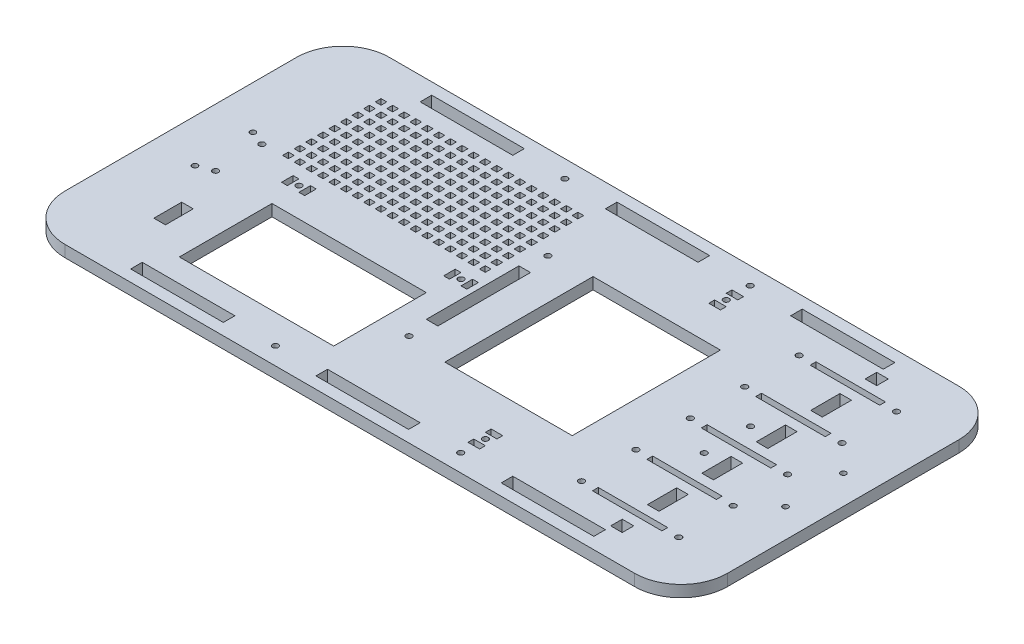
SolidWorks part; units mm, degrees
ref_plane "Front Plane" through (0, 0, 0) normal (0, 0, 1) x (1, 0, 0)
ref_plane "Top Plane" through (0, 0, 0) normal (0, 1, 0) x (1, 0, 0)
ref_plane "Right Plane" through (0, 0, 0) normal (1, 0, 0) x (0, 0, -1)
sketch "Sketch3" plane through (0, 0, 0) normal (0, 1, 0) x (1, 0, 0)
  line L1 (-156.21, -88.9) -> (156.21, -88.9)
  line L2 (-181.61, -63.5) -> (-181.61, 63.5)
  line L3 (-156.21, 88.9) -> (156.21, 88.9)
  line L4 (181.61, -63.5) -> (181.61, 63.5)
  line L5 (-181.61, -88.9) -> (181.61, 88.9) construction
  line L6 (-181.61, 88.9) -> (181.61, -88.9) construction
  arc A0 (156.21, -88.9) -> (181.61, -63.5) centre (156.21, -63.5) ccw
  arc A1 (156.21, 88.9) -> (181.61, 63.5) centre (156.21, 63.5) cw
  arc A2 (-156.21, -88.9) -> (-181.61, -63.5) centre (-156.21, -63.5) cw
  arc A3 (-181.61, 63.5) -> (-156.21, 88.9) centre (-156.21, 63.5) cw
  point P0 (0, 0)
  dimension "D3" = 25.4
  dimension "D1" = 177.8
  dimension "D2" = 363.22
extrude "BaseExtrude" add sketch "Sketch3" against normal blind 6.35
sketch "Sketch6" plane through (0, 0, 0) normal (0, 1, 0) x (1, 0, 0)
  line L0 (-181.61, 0) -> (181.61, 0) construction
  line L1 (-181.61, 63.5) -> (-181.61, -63.5) construction
  line L2 (181.61, -63.5) -> (181.61, 63.5) construction
  line L3 (0, -88.9) -> (0, 88.9) construction
  line L4 (-156.21, -88.9) -> (156.21, -88.9) construction
  line L5 (156.21, 88.9) -> (-156.21, 88.9) construction
  line L6 (3.937, 0) -> (3.937, 19.6413) construction
  circle A0 centre (-157.988, 15.875) radius 1.5
  circle A1 centre (-157.988, -15.875) radius 1.5
  circle A2 centre (165.862, -15.875) radius 1.5
  circle A3 centre (165.862, 15.875) radius 1.5
  dimension "D2" = 3
  dimension "D1" = 23.622
  dimension "D3" = 15.875
  dimension "D4" = 161.925
extrude "MainMountCut" cut sketch "Sketch6" against normal up to surface (6.35 mm away) up to face at (0, -6.35, 0)
sketch "Sketch7" plane through (0, 0, 0) normal (0, 1, 0) x (1, 0, 0)
  line L0 (76.6233, 79.375) -> (25.8233, 79.375) construction
  line L1 (127.4233, -82.55) -> (76.6233, -82.55)
  line L2 (127.4233, -82.55) -> (127.4233, -76.2)
  line L3 (127.4233, -76.2) -> (76.6233, -76.2)
  line L4 (76.6233, -82.55) -> (76.6233, -76.2)
  line L5 (25.8233, -82.55) -> (-24.9767, -82.55)
  line L6 (25.8233, -82.55) -> (25.8233, -76.2)
  line L7 (25.8233, -76.2) -> (-24.9767, -76.2)
  line L8 (-24.9767, -82.55) -> (-24.9767, -76.2)
  line L9 (-75.7767, -82.55) -> (-126.5767, -82.55)
  line L10 (-75.7767, -82.55) -> (-75.7767, -76.2)
  line L11 (-75.7767, -76.2) -> (-126.5767, -76.2)
  line L12 (-126.5767, -82.55) -> (-126.5767, -76.2)
  line L13 (127.4233, 76.2) -> (76.6233, 76.2)
  line L14 (127.4233, 76.2) -> (127.4233, 82.55)
  line L15 (127.4233, 82.55) -> (76.6233, 82.55)
  line L16 (76.6233, 76.2) -> (76.6233, 82.55)
  line L17 (25.8233, 76.2) -> (-24.9767, 76.2)
  line L18 (25.8233, 76.2) -> (25.8233, 82.55)
  line L19 (25.8233, 82.55) -> (-24.9767, 82.55)
  line L20 (-24.9767, 76.2) -> (-24.9767, 82.55)
  line L21 (-75.7767, 76.2) -> (-126.5767, 76.2)
  line L22 (-75.7767, 76.2) -> (-75.7767, 82.55)
  line L23 (-75.7767, 82.55) -> (-126.5767, 82.55)
  line L24 (-126.5767, 76.2) -> (-126.5767, 82.55)
  line L25 (-24.9767, 79.375) -> (-75.7767, 79.375) construction
  line L26 (-75.7767, -79.375) -> (-24.9767, -79.375) construction
  line L27 (76.6233, -79.375) -> (25.8233, -79.375) construction
  line L28 (181.61, -63.5) -> (181.61, 63.5) construction
  line L32 (-156.21, -88.9) -> (156.21, -88.9) construction
  line L35 (156.21, 88.9) -> (-156.21, 88.9) construction
  circle A0 centre (51.2233, 79.375) radius 1.6
  circle A1 centre (-50.3767, 79.375) radius 1.6
  circle A2 centre (-50.3767, -79.375) radius 1.6
  circle A3 centre (51.2233, -79.375) radius 1.6
  dimension "D5" = 3.2
  dimension "D1" = 50.8
  dimension "D2" = 6.35
  dimension "D3" = 6.35
  dimension "D4" = 6.35
  dimension "D6" = 54.1867
extrude "WallCut" cut sketch "Sketch7" against normal through all
sketch "Sketch8" plane through (0, 0, 0) normal (0, 1, 0) x (1, 0, 0)
  line L0 (124.46, -58.1025) -> (124.46, -31.4325) construction
  line L1 (143.51, -61.2775) -> (105.41, -61.2775)
  line L2 (143.51, -61.2775) -> (143.51, -58.1025)
  line L3 (143.51, -58.1025) -> (105.41, -58.1025)
  line L4 (105.41, -61.2775) -> (105.41, -58.1025)
  line L5 (143.51, -31.4325) -> (105.41, -31.4325)
  line L6 (143.51, -31.4325) -> (143.51, -28.2575)
  line L7 (143.51, -28.2575) -> (105.41, -28.2575)
  line L8 (105.41, -31.4325) -> (105.41, -28.2575)
  line L9 (143.51, -1.5875) -> (105.41, -1.5875)
  line L10 (143.51, -1.5875) -> (143.51, 1.5875)
  line L11 (143.51, 1.5875) -> (105.41, 1.5875)
  line L12 (105.41, -1.5875) -> (105.41, 1.5875)
  line L13 (143.51, 28.2575) -> (105.41, 28.2575)
  line L14 (143.51, 28.2575) -> (143.51, 31.4325)
  line L15 (143.51, 31.4325) -> (105.41, 31.4325)
  line L16 (105.41, 28.2575) -> (105.41, 31.4325)
  line L17 (143.51, 58.1025) -> (105.41, 58.1025)
  line L18 (143.51, 58.1025) -> (143.51, 61.2775)
  line L19 (143.51, 61.2775) -> (105.41, 61.2775)
  line L20 (105.41, 58.1025) -> (105.41, 61.2775)
  line L21 (124.46, -28.2575) -> (124.46, -1.5875) construction
  line L22 (124.46, -61.2775) -> (124.46, -76.2) construction
  line L23 (124.46, 1.5875) -> (124.46, 28.2575) construction
  line L24 (124.46, 31.4325) -> (124.46, 58.1025) construction
  line L25 (127.4233, -76.2) -> (76.6233, -76.2) construction
  line L26 (124.46, 61.2775) -> (124.46, 76.2) construction
  line L27 (76.6233, 76.2) -> (127.4233, 76.2) construction
  line L28 (181.61, -63.5) -> (181.61, 63.5) construction
  line L29 (143.51, -59.69) -> (151.13, -59.69) construction
  line L30 (151.13, -59.69) -> (151.13, 59.69) construction
  line L31 (151.13, 59.69) -> (143.51, 59.69) construction
  line L32 (143.51, 29.845) -> (151.13, 29.845) construction
  line L33 (143.51, 0) -> (151.13, 0) construction
  line L34 (143.51, -29.845) -> (151.13, -29.845) construction
  line L35 (105.41, -59.69) -> (97.79, -59.69) construction
  line L36 (97.79, -59.69) -> (97.79, 59.69) construction
  line L37 (97.79, 59.69) -> (105.41, 59.69) construction
  line L38 (105.41, 29.845) -> (97.79, 29.845) construction
  line L39 (105.41, 0) -> (97.79, 0) construction
  line L40 (105.41, -29.845) -> (97.79, -29.845) construction
  circle A0 centre (151.13, -59.69) radius 1.6
  circle A1 centre (151.13, -29.845) radius 1.6
  circle A2 centre (151.13, 0) radius 1.6
  circle A3 centre (151.13, 29.845) radius 1.6
  circle A4 centre (151.13, 59.69) radius 1.6
  circle A5 centre (97.79, 59.69) radius 1.6
  circle A6 centre (97.79, 29.845) radius 1.6
  circle A7 centre (97.79, 0) radius 1.6
  circle A8 centre (97.79, -29.845) radius 1.6
  circle A9 centre (97.79, -59.69) radius 1.6
  dimension "D6" = 3.2
  dimension "D1" = 3.175
  dimension "D2" = 26.67
  dimension "D3" = 38.1
  dimension "D4" = 57.15
  dimension "D5" = 7.62
extrude "WireMountCut" cut sketch "Sketch8" against normal through all
sketch "Sketch9" plane through (0, 0, 0) normal (0, 1, 0) x (1, 0, 0)
  line L0 (118.11, -12.7) -> (118.11, 12.7) construction
  line L1 (-149.86, -12.7) -> (-149.86, 12.7) construction
  line L2 (-149.86, 12.7) -> (118.11, 12.7) construction
  line L3 (118.11, -12.7) -> (-149.86, -12.7) construction
  line L4 (118.11, -12.7) -> (118.11, -88.9) construction
  line L5 (-156.21, -88.9) -> (156.21, -88.9) construction
  line L6 (118.11, 12.7) -> (118.11, 88.9) construction
  line L7 (156.21, 88.9) -> (-156.21, 88.9) construction
  line L8 (-181.61, 63.5) -> (-181.61, -63.5) construction
  line L9 (181.61, -63.5) -> (181.61, 63.5) construction
  circle A0 centre (118.11, 12.7) radius 1.6
  circle A1 centre (118.11, -12.7) radius 1.6
  circle A2 centre (-149.86, -12.7) radius 1.6
  circle A3 centre (-149.86, 12.7) radius 1.6
  dimension "D1" = 3.2
  dimension "D2" = 76.2
  dimension "D3" = 31.75
  dimension "D4" = 63.5
extrude "Cut-Extrude3" cut sketch "Sketch9" against normal through all
sketch "Sketch11" plane through (0, 0, 0) normal (0, 1, 0) x (1, 0, 0)
  line L0 (54.61, 72.39) -> (48.26, 72.39)
  line L1 (54.61, -69.215) -> (54.61, -62.865) construction
  line L2 (54.61, 59.69) -> (48.26, 59.69)
  line L3 (54.61, -72.39) -> (54.61, -69.215)
  line L4 (54.61, -69.215) -> (48.26, -69.215)
  line L5 (181.61, 0) -> (-181.61, 0) construction
  line L6 (181.61, -63.5) -> (181.61, 63.5) construction
  line L7 (-181.61, 63.5) -> (-181.61, -63.5) construction
  line L8 (51.435, 66.04) -> (51.435, 62.865) construction
  line L9 (-15.24, -25.4) -> (-21.59, -25.4)
  line L10 (-15.24, -25.4) -> (-15.24, 25.4)
  line L11 (-15.24, 25.4) -> (-21.59, 25.4)
  line L12 (-21.59, -25.4) -> (-21.59, 25.4)
  line L13 (48.26, -72.39) -> (48.26, -69.215)
  line L14 (54.61, -62.865) -> (48.26, -62.865)
  line L15 (54.61, -62.865) -> (54.61, -59.69)
  line L17 (48.26, -62.865) -> (48.26, -59.69)
  line L18 (51.435, -69.215) -> (51.435, -66.04) construction
  line L19 (48.26, -69.215) -> (48.26, -62.865) construction
  line L20 (51.435, -66.04) -> (51.435, -62.865) construction
  line L22 (48.26, 69.215) -> (48.26, 62.865) construction
  line L23 (51.435, 69.215) -> (51.435, 66.04) construction
  line L24 (54.61, 69.215) -> (54.61, 62.865) construction
  line L25 (48.26, 62.865) -> (48.26, 59.69)
  line L27 (54.61, 62.865) -> (54.61, 59.69)
  line L28 (54.61, 62.865) -> (48.26, 62.865)
  line L29 (48.26, 72.39) -> (48.26, 69.215)
  line L30 (54.61, 69.215) -> (48.26, 69.215)
  line L31 (54.61, 72.39) -> (54.61, 69.215)
  line L33 (51.435, -66.04) -> (51.435, -62.865) construction
  line L34 (-18.415, -25.4) -> (-18.415, -38.1) construction
  line L35 (-18.415, 25.4) -> (-18.415, 38.1) construction
  line L36 (54.61, -72.39) -> (48.26, -72.39)
  line L37 (54.61, -59.69) -> (48.26, -59.69)
  circle A0 centre (51.435, -66.04) radius 1.6
  circle A1 centre (51.435, 66.04) radius 1.6
  circle A2 centre (-18.415, -38.1) radius 1.6
  circle A3 centre (-18.415, 38.1) radius 1.6
  point P45 (-15.24, 0)
  dimension "D4" = 50.8
  dimension "D2" = 3.2
  dimension "D9" = 3.2
  dimension "D1" = 12.7
  dimension "D6" = 63.5
  dimension "D7" = 50.8
  dimension "D8" = 12.7
extrude "Cut-Extrude4" cut sketch "Sketch11" against normal through all
sketch "Sketch13" plane through (0, 0, 0) normal (0, 1, 0) x (1, 0, 0)
  line L0 (-123.2154, 6.35) -> (-116.8654, 6.35) construction
  line L1 (-24.7904, 6.35) -> (-27.9654, 6.35)
  line L2 (-24.7904, 6.35) -> (-24.7904, 0)
  line L3 (-24.7904, 0) -> (-27.9654, 0)
  line L4 (-27.9654, 6.35) -> (-27.9654, 0)
  line L5 (-34.3154, 6.35) -> (-37.4904, 6.35)
  line L6 (-34.3154, 6.35) -> (-34.3154, 0)
  line L7 (-34.3154, 0) -> (-37.4904, 0)
  line L8 (-37.4904, 6.35) -> (-37.4904, 0)
  line L9 (-113.6904, 0) -> (-116.8654, 0)
  line L10 (-113.6904, 0) -> (-113.6904, 6.35)
  line L11 (-113.6904, 6.35) -> (-116.8654, 6.35)
  line L12 (-116.8654, 0) -> (-116.8654, 6.35)
  line L13 (-123.2154, 0) -> (-126.3904, 0)
  line L14 (-123.2154, 0) -> (-123.2154, 6.35)
  line L15 (-123.2154, 6.35) -> (-126.3904, 6.35)
  line L16 (-126.3904, 0) -> (-126.3904, 6.35)
  line L17 (-123.2154, 0) -> (-116.8654, 0) construction
  line L18 (-34.3154, 0) -> (-27.9654, 0) construction
  line L19 (-34.3154, 6.35) -> (-27.9654, 6.35) construction
  line L20 (-34.3154, 3.175) -> (-31.1404, 3.175) construction
  line L21 (-31.1404, 3.175) -> (-27.9654, 3.175) construction
  line L22 (-123.2154, 3.175) -> (-120.0404, 3.175) construction
  line L23 (-120.0404, 3.175) -> (-116.8654, 3.175) construction
  line L25 (-75.7767, -76.2) -> (-126.5767, -76.2) construction
  line L26 (-21.59, 25.4) -> (-21.59, -25.4) construction
  circle A0 centre (-120.0404, 3.175) radius 1.6
  circle A1 centre (-31.1404, 3.175) radius 1.6
  dimension "D3" = 3.2
  dimension "D1" = 3.175
  dimension "D2" = 6.35
  dimension "D4" = 76.2
  dimension "D5" = 6.35
  dimension "D6" = 3.2004
  dimension "D7" = 88.9
extrude "Cut-Extrude5" cut sketch "Sketch13" against normal through all
sketch "Sketch14" plane through (0, 0, 0) normal (0, 1, 0) x (1, 0, 0)
  line L0 (-137.9819, -44.45) -> (-144.3319, -44.45) construction
  line L1 (-137.9819, -52.07) -> (-144.3319, -52.07)
  line L2 (-137.9819, -52.07) -> (-137.9819, -36.83)
  line L3 (-137.9819, -36.83) -> (-144.3319, -36.83)
  line L4 (-144.3319, -52.07) -> (-144.3319, -36.83)
  line L5 (-75.7767, -76.2) -> (-126.5767, -76.2) construction
  line L6 (-181.61, 63.5) -> (-181.61, -63.5) construction
  dimension "D1" = 15.24
  dimension "D2" = 6.35
  dimension "D3" = 31.75
  dimension "D4" = 37.2781
extrude "Cut-Extrude6" cut sketch "Sketch14" against normal through all
ref_plane "Plane1" through (0, 0, 44.45) normal (0, 0, -1) x (-1, 0, 0)
sketch "Sketch15" plane through (0, 0, 0) normal (0, 1, 0) x (1, 0, 0)
  line L0 (181.61, 0) -> (73.66, 0) construction
  line L1 (73.66, 40.64) -> (3.81, 40.64)
  line L2 (73.66, 40.64) -> (73.66, -40.64)
  line L3 (73.66, -40.64) -> (3.81, -40.64)
  line L4 (3.81, 40.64) -> (3.81, -40.64)
  line L5 (181.61, -63.5) -> (181.61, 63.5) construction
  line L6 (48.26, 59.69) -> (54.61, 59.69) construction
  line L7 (-15.24, -25.4) -> (-15.24, 25.4) construction
  line L8 (-37.4904, 0) -> (-34.3154, 0) construction
  line L9 (-34.29, -12.7) -> (-118.9319, -12.7)
  line L10 (-34.29, -12.7) -> (-34.29, -63.5)
  line L11 (-34.29, -63.5) -> (-118.9319, -63.5)
  line L12 (-118.9319, -12.7) -> (-118.9319, -63.5)
  line L13 (-75.7767, -76.2) -> (-126.5767, -76.2) construction
  line L14 (-137.9819, -52.07) -> (-137.9819, -36.83) construction
  line L15 (-21.59, 25.4) -> (-21.59, -25.4) construction
  line L16 (-34.0808, 67.0276) -> (-34.0808, 63.8526)
  line L17 (-27.7308, 67.0276) -> (-30.9058, 67.0276)
  line L18 (-27.7308, 67.0276) -> (-27.7308, 63.8526)
  line L19 (-27.7308, 63.8526) -> (-30.9058, 63.8526)
  line L20 (-30.9058, 67.0276) -> (-30.9058, 63.8526)
  line L21 (-34.0808, 67.0276) -> (-37.2558, 67.0276)
  line L22 (-37.2558, 67.0276) -> (-37.2558, 63.8526)
  line L23 (-34.0808, 63.8526) -> (-37.2558, 63.8526)
  line L24 (-40.4308, 67.0276) -> (-40.4308, 63.8526)
  line L25 (-40.4308, 67.0276) -> (-43.6058, 67.0276)
  line L26 (-43.6058, 67.0276) -> (-43.6058, 63.8526)
  line L27 (-40.4308, 63.8526) -> (-43.6058, 63.8526)
  line L28 (-46.7808, 67.0276) -> (-46.7808, 63.8526)
  line L29 (-46.7808, 67.0276) -> (-49.9558, 67.0276)
  line L30 (-49.9558, 67.0276) -> (-49.9558, 63.8526)
  line L31 (-46.7808, 63.8526) -> (-49.9558, 63.8526)
  line L32 (-53.1308, 67.0276) -> (-53.1308, 63.8526)
  line L33 (-53.1308, 67.0276) -> (-56.3058, 67.0276)
  line L34 (-56.3058, 67.0276) -> (-56.3058, 63.8526)
  line L35 (-53.1308, 63.8526) -> (-56.3058, 63.8526)
  line L36 (-59.4808, 67.0276) -> (-59.4808, 63.8526)
  line L37 (-59.4808, 67.0276) -> (-62.6558, 67.0276)
  line L38 (-62.6558, 67.0276) -> (-62.6558, 63.8526)
  line L39 (-59.4808, 63.8526) -> (-62.6558, 63.8526)
  line L40 (-65.8308, 67.0276) -> (-65.8308, 63.8526)
  line L41 (-65.8308, 67.0276) -> (-69.0058, 67.0276)
  line L42 (-69.0058, 67.0276) -> (-69.0058, 63.8526)
  line L43 (-65.8308, 63.8526) -> (-69.0058, 63.8526)
  line L44 (-72.1808, 67.0276) -> (-72.1808, 63.8526)
  line L45 (-72.1808, 67.0276) -> (-75.3558, 67.0276)
  line L46 (-75.3558, 67.0276) -> (-75.3558, 63.8526)
  line L47 (-72.1808, 63.8526) -> (-75.3558, 63.8526)
  line L48 (-78.5308, 67.0276) -> (-78.5308, 63.8526)
  line L49 (-78.5308, 67.0276) -> (-81.7058, 67.0276)
  line L50 (-81.7058, 67.0276) -> (-81.7058, 63.8526)
  line L51 (-78.5308, 63.8526) -> (-81.7058, 63.8526)
  line L52 (-84.8808, 67.0276) -> (-84.8808, 63.8526)
  line L53 (-84.8808, 67.0276) -> (-88.0558, 67.0276)
  line L54 (-88.0558, 67.0276) -> (-88.0558, 63.8526)
  line L55 (-84.8808, 63.8526) -> (-88.0558, 63.8526)
  line L56 (-91.2308, 67.0276) -> (-91.2308, 63.8526)
  line L57 (-91.2308, 67.0276) -> (-94.4058, 67.0276)
  line L58 (-94.4058, 67.0276) -> (-94.4058, 63.8526)
  line L59 (-91.2308, 63.8526) -> (-94.4058, 63.8526)
  line L60 (-97.5808, 67.0276) -> (-97.5808, 63.8526)
  line L61 (-97.5808, 67.0276) -> (-100.7558, 67.0276)
  line L62 (-100.7558, 67.0276) -> (-100.7558, 63.8526)
  line L63 (-97.5808, 63.8526) -> (-100.7558, 63.8526)
  line L64 (-103.9308, 67.0276) -> (-103.9308, 63.8526)
  line L65 (-103.9308, 67.0276) -> (-107.1058, 67.0276)
  line L66 (-107.1058, 67.0276) -> (-107.1058, 63.8526)
  line L67 (-103.9308, 63.8526) -> (-107.1058, 63.8526)
  line L68 (-110.2808, 67.0276) -> (-110.2808, 63.8526)
  line L69 (-110.2808, 67.0276) -> (-113.4558, 67.0276)
  line L70 (-113.4558, 67.0276) -> (-113.4558, 63.8526)
  line L71 (-110.2808, 63.8526) -> (-113.4558, 63.8526)
  line L72 (-116.6308, 67.0276) -> (-116.6308, 63.8526)
  line L73 (-116.6308, 67.0276) -> (-119.8058, 67.0276)
  line L74 (-119.8058, 67.0276) -> (-119.8058, 63.8526)
  line L75 (-116.6308, 63.8526) -> (-119.8058, 63.8526)
  line L76 (-122.9808, 67.0276) -> (-122.9808, 63.8526)
  line L77 (-122.9808, 67.0276) -> (-126.1558, 67.0276)
  line L78 (-126.1558, 67.0276) -> (-126.1558, 63.8526)
  line L79 (-122.9808, 63.8526) -> (-126.1558, 63.8526)
  line L80 (-129.3308, 67.0276) -> (-129.3308, 63.8526)
  line L81 (-129.3308, 67.0276) -> (-132.5058, 67.0276)
  line L82 (-132.5058, 67.0276) -> (-132.5058, 63.8526)
  line L83 (-129.3308, 63.8526) -> (-132.5058, 63.8526)
  line L84 (-135.6808, 67.0276) -> (-135.6808, 63.8526)
  line L85 (-135.6808, 67.0276) -> (-138.8558, 67.0276)
  line L86 (-138.8558, 67.0276) -> (-138.8558, 63.8526)
  line L87 (-135.6808, 63.8526) -> (-138.8558, 63.8526)
  line L88 (-34.0808, 60.6776) -> (-34.0808, 57.5026)
  line L89 (-34.0808, 60.6776) -> (-37.2558, 60.6776)
  line L90 (-37.2558, 60.6776) -> (-37.2558, 57.5026)
  line L91 (-34.0808, 57.5026) -> (-37.2558, 57.5026)
  line L92 (-40.4308, 60.6776) -> (-40.4308, 57.5026)
  line L93 (-40.4308, 60.6776) -> (-43.6058, 60.6776)
  line L94 (-43.6058, 60.6776) -> (-43.6058, 57.5026)
  line L95 (-40.4308, 57.5026) -> (-43.6058, 57.5026)
  line L96 (-46.7808, 60.6776) -> (-46.7808, 57.5026)
  line L97 (-46.7808, 60.6776) -> (-49.9558, 60.6776)
  line L98 (-49.9558, 60.6776) -> (-49.9558, 57.5026)
  line L99 (-46.7808, 57.5026) -> (-49.9558, 57.5026)
  line L100 (-53.1308, 60.6776) -> (-53.1308, 57.5026)
  line L101 (-53.1308, 60.6776) -> (-56.3058, 60.6776)
  line L102 (-56.3058, 60.6776) -> (-56.3058, 57.5026)
  line L103 (-53.1308, 57.5026) -> (-56.3058, 57.5026)
  line L104 (-59.4808, 60.6776) -> (-59.4808, 57.5026)
  line L105 (-59.4808, 60.6776) -> (-62.6558, 60.6776)
  line L106 (-62.6558, 60.6776) -> (-62.6558, 57.5026)
  line L107 (-59.4808, 57.5026) -> (-62.6558, 57.5026)
  line L108 (-65.8308, 60.6776) -> (-65.8308, 57.5026)
  line L109 (-65.8308, 60.6776) -> (-69.0058, 60.6776)
  line L110 (-69.0058, 60.6776) -> (-69.0058, 57.5026)
  line L111 (-65.8308, 57.5026) -> (-69.0058, 57.5026)
  line L112 (-72.1808, 60.6776) -> (-72.1808, 57.5026)
  line L113 (-72.1808, 60.6776) -> (-75.3558, 60.6776)
  line L114 (-75.3558, 60.6776) -> (-75.3558, 57.5026)
  line L115 (-72.1808, 57.5026) -> (-75.3558, 57.5026)
  line L116 (-78.5308, 60.6776) -> (-78.5308, 57.5026)
  line L117 (-78.5308, 60.6776) -> (-81.7058, 60.6776)
  line L118 (-81.7058, 60.6776) -> (-81.7058, 57.5026)
  line L119 (-78.5308, 57.5026) -> (-81.7058, 57.5026)
  line L120 (-84.8808, 60.6776) -> (-84.8808, 57.5026)
  line L121 (-84.8808, 60.6776) -> (-88.0558, 60.6776)
  line L122 (-88.0558, 60.6776) -> (-88.0558, 57.5026)
  line L123 (-84.8808, 57.5026) -> (-88.0558, 57.5026)
  line L124 (-91.2308, 60.6776) -> (-91.2308, 57.5026)
  line L125 (-91.2308, 60.6776) -> (-94.4058, 60.6776)
  line L126 (-94.4058, 60.6776) -> (-94.4058, 57.5026)
  line L127 (-91.2308, 57.5026) -> (-94.4058, 57.5026)
  line L128 (-97.5808, 60.6776) -> (-97.5808, 57.5026)
  line L129 (-97.5808, 60.6776) -> (-100.7558, 60.6776)
  line L130 (-100.7558, 60.6776) -> (-100.7558, 57.5026)
  line L131 (-97.5808, 57.5026) -> (-100.7558, 57.5026)
  line L132 (-103.9308, 60.6776) -> (-103.9308, 57.5026)
  line L133 (-103.9308, 60.6776) -> (-107.1058, 60.6776)
  line L134 (-107.1058, 60.6776) -> (-107.1058, 57.5026)
  line L135 (-103.9308, 57.5026) -> (-107.1058, 57.5026)
  line L136 (-110.2808, 60.6776) -> (-110.2808, 57.5026)
  line L137 (-110.2808, 60.6776) -> (-113.4558, 60.6776)
  line L138 (-113.4558, 60.6776) -> (-113.4558, 57.5026)
  line L139 (-110.2808, 57.5026) -> (-113.4558, 57.5026)
  line L140 (-116.6308, 60.6776) -> (-116.6308, 57.5026)
  line L141 (-116.6308, 60.6776) -> (-119.8058, 60.6776)
  line L142 (-119.8058, 60.6776) -> (-119.8058, 57.5026)
  line L143 (-116.6308, 57.5026) -> (-119.8058, 57.5026)
  line L144 (-122.9808, 60.6776) -> (-122.9808, 57.5026)
  line L145 (-122.9808, 60.6776) -> (-126.1558, 60.6776)
  line L146 (-126.1558, 60.6776) -> (-126.1558, 57.5026)
  line L147 (-122.9808, 57.5026) -> (-126.1558, 57.5026)
  line L148 (-129.3308, 60.6776) -> (-129.3308, 57.5026)
  line L149 (-129.3308, 60.6776) -> (-132.5058, 60.6776)
  line L150 (-132.5058, 60.6776) -> (-132.5058, 57.5026)
  line L151 (-129.3308, 57.5026) -> (-132.5058, 57.5026)
  line L152 (-135.6808, 60.6776) -> (-135.6808, 57.5026)
  line L153 (-135.6808, 60.6776) -> (-138.8558, 60.6776)
  line L154 (-138.8558, 60.6776) -> (-138.8558, 57.5026)
  line L155 (-135.6808, 57.5026) -> (-138.8558, 57.5026)
  line L156 (-34.0808, 54.3276) -> (-34.0808, 51.1526)
  line L157 (-34.0808, 54.3276) -> (-37.2558, 54.3276)
  line L158 (-37.2558, 54.3276) -> (-37.2558, 51.1526)
  line L159 (-34.0808, 51.1526) -> (-37.2558, 51.1526)
  line L160 (-40.4308, 54.3276) -> (-40.4308, 51.1526)
  line L161 (-40.4308, 54.3276) -> (-43.6058, 54.3276)
  line L162 (-43.6058, 54.3276) -> (-43.6058, 51.1526)
  line L163 (-40.4308, 51.1526) -> (-43.6058, 51.1526)
  line L164 (-46.7808, 54.3276) -> (-46.7808, 51.1526)
  line L165 (-46.7808, 54.3276) -> (-49.9558, 54.3276)
  line L166 (-49.9558, 54.3276) -> (-49.9558, 51.1526)
  line L167 (-46.7808, 51.1526) -> (-49.9558, 51.1526)
  line L168 (-53.1308, 54.3276) -> (-53.1308, 51.1526)
  line L169 (-53.1308, 54.3276) -> (-56.3058, 54.3276)
  line L170 (-56.3058, 54.3276) -> (-56.3058, 51.1526)
  line L171 (-53.1308, 51.1526) -> (-56.3058, 51.1526)
  line L172 (-59.4808, 54.3276) -> (-59.4808, 51.1526)
  line L173 (-59.4808, 54.3276) -> (-62.6558, 54.3276)
  line L174 (-62.6558, 54.3276) -> (-62.6558, 51.1526)
  line L175 (-59.4808, 51.1526) -> (-62.6558, 51.1526)
  line L176 (-65.8308, 54.3276) -> (-65.8308, 51.1526)
  line L177 (-65.8308, 54.3276) -> (-69.0058, 54.3276)
  line L178 (-69.0058, 54.3276) -> (-69.0058, 51.1526)
  line L179 (-65.8308, 51.1526) -> (-69.0058, 51.1526)
  line L180 (-72.1808, 54.3276) -> (-72.1808, 51.1526)
  line L181 (-72.1808, 54.3276) -> (-75.3558, 54.3276)
  line L182 (-75.3558, 54.3276) -> (-75.3558, 51.1526)
  line L183 (-72.1808, 51.1526) -> (-75.3558, 51.1526)
  line L184 (-78.5308, 54.3276) -> (-78.5308, 51.1526)
  line L185 (-78.5308, 54.3276) -> (-81.7058, 54.3276)
  line L186 (-81.7058, 54.3276) -> (-81.7058, 51.1526)
  line L187 (-78.5308, 51.1526) -> (-81.7058, 51.1526)
  line L188 (-84.8808, 54.3276) -> (-84.8808, 51.1526)
  line L189 (-84.8808, 54.3276) -> (-88.0558, 54.3276)
  line L190 (-88.0558, 54.3276) -> (-88.0558, 51.1526)
  line L191 (-84.8808, 51.1526) -> (-88.0558, 51.1526)
  line L192 (-91.2308, 54.3276) -> (-91.2308, 51.1526)
  line L193 (-91.2308, 54.3276) -> (-94.4058, 54.3276)
  line L194 (-94.4058, 54.3276) -> (-94.4058, 51.1526)
  line L195 (-91.2308, 51.1526) -> (-94.4058, 51.1526)
  line L196 (-97.5808, 54.3276) -> (-97.5808, 51.1526)
  line L197 (-97.5808, 54.3276) -> (-100.7558, 54.3276)
  line L198 (-100.7558, 54.3276) -> (-100.7558, 51.1526)
  line L199 (-97.5808, 51.1526) -> (-100.7558, 51.1526)
  line L200 (-103.9308, 54.3276) -> (-103.9308, 51.1526)
  line L201 (-103.9308, 54.3276) -> (-107.1058, 54.3276)
  line L202 (-107.1058, 54.3276) -> (-107.1058, 51.1526)
  line L203 (-103.9308, 51.1526) -> (-107.1058, 51.1526)
  line L204 (-110.2808, 54.3276) -> (-110.2808, 51.1526)
  line L205 (-110.2808, 54.3276) -> (-113.4558, 54.3276)
  line L206 (-113.4558, 54.3276) -> (-113.4558, 51.1526)
  line L207 (-110.2808, 51.1526) -> (-113.4558, 51.1526)
  line L208 (-116.6308, 54.3276) -> (-116.6308, 51.1526)
  line L209 (-116.6308, 54.3276) -> (-119.8058, 54.3276)
  line L210 (-119.8058, 54.3276) -> (-119.8058, 51.1526)
  line L211 (-116.6308, 51.1526) -> (-119.8058, 51.1526)
  line L212 (-122.9808, 54.3276) -> (-122.9808, 51.1526)
  line L213 (-122.9808, 54.3276) -> (-126.1558, 54.3276)
  line L214 (-126.1558, 54.3276) -> (-126.1558, 51.1526)
  line L215 (-122.9808, 51.1526) -> (-126.1558, 51.1526)
  line L216 (-129.3308, 54.3276) -> (-129.3308, 51.1526)
  line L217 (-129.3308, 54.3276) -> (-132.5058, 54.3276)
  line L218 (-132.5058, 54.3276) -> (-132.5058, 51.1526)
  line L219 (-129.3308, 51.1526) -> (-132.5058, 51.1526)
  line L220 (-135.6808, 54.3276) -> (-135.6808, 51.1526)
  line L221 (-135.6808, 54.3276) -> (-138.8558, 54.3276)
  line L222 (-138.8558, 54.3276) -> (-138.8558, 51.1526)
  line L223 (-135.6808, 51.1526) -> (-138.8558, 51.1526)
  line L224 (-34.0808, 47.9776) -> (-34.0808, 44.8026)
  line L225 (-34.0808, 47.9776) -> (-37.2558, 47.9776)
  line L226 (-37.2558, 47.9776) -> (-37.2558, 44.8026)
  line L227 (-34.0808, 44.8026) -> (-37.2558, 44.8026)
  line L228 (-40.4308, 47.9776) -> (-40.4308, 44.8026)
  line L229 (-40.4308, 47.9776) -> (-43.6058, 47.9776)
  line L230 (-43.6058, 47.9776) -> (-43.6058, 44.8026)
  line L231 (-40.4308, 44.8026) -> (-43.6058, 44.8026)
  line L232 (-46.7808, 47.9776) -> (-46.7808, 44.8026)
  line L233 (-46.7808, 47.9776) -> (-49.9558, 47.9776)
  line L234 (-49.9558, 47.9776) -> (-49.9558, 44.8026)
  line L235 (-46.7808, 44.8026) -> (-49.9558, 44.8026)
  line L236 (-53.1308, 47.9776) -> (-53.1308, 44.8026)
  line L237 (-53.1308, 47.9776) -> (-56.3058, 47.9776)
  line L238 (-56.3058, 47.9776) -> (-56.3058, 44.8026)
  line L239 (-53.1308, 44.8026) -> (-56.3058, 44.8026)
  line L240 (-59.4808, 47.9776) -> (-59.4808, 44.8026)
  line L241 (-59.4808, 47.9776) -> (-62.6558, 47.9776)
  line L242 (-62.6558, 47.9776) -> (-62.6558, 44.8026)
  line L243 (-59.4808, 44.8026) -> (-62.6558, 44.8026)
  line L244 (-65.8308, 47.9776) -> (-65.8308, 44.8026)
  line L245 (-65.8308, 47.9776) -> (-69.0058, 47.9776)
  line L246 (-69.0058, 47.9776) -> (-69.0058, 44.8026)
  line L247 (-65.8308, 44.8026) -> (-69.0058, 44.8026)
  line L248 (-72.1808, 47.9776) -> (-72.1808, 44.8026)
  line L249 (-72.1808, 47.9776) -> (-75.3558, 47.9776)
  line L250 (-75.3558, 47.9776) -> (-75.3558, 44.8026)
  line L251 (-72.1808, 44.8026) -> (-75.3558, 44.8026)
  line L252 (-78.5308, 47.9776) -> (-78.5308, 44.8026)
  line L253 (-78.5308, 47.9776) -> (-81.7058, 47.9776)
  line L254 (-81.7058, 47.9776) -> (-81.7058, 44.8026)
  line L255 (-78.5308, 44.8026) -> (-81.7058, 44.8026)
  line L256 (-84.8808, 47.9776) -> (-84.8808, 44.8026)
  line L257 (-84.8808, 47.9776) -> (-88.0558, 47.9776)
  line L258 (-88.0558, 47.9776) -> (-88.0558, 44.8026)
  line L259 (-84.8808, 44.8026) -> (-88.0558, 44.8026)
  line L260 (-91.2308, 47.9776) -> (-91.2308, 44.8026)
  line L261 (-91.2308, 47.9776) -> (-94.4058, 47.9776)
  line L262 (-94.4058, 47.9776) -> (-94.4058, 44.8026)
  line L263 (-91.2308, 44.8026) -> (-94.4058, 44.8026)
  line L264 (-97.5808, 47.9776) -> (-97.5808, 44.8026)
  line L265 (-97.5808, 47.9776) -> (-100.7558, 47.9776)
  line L266 (-100.7558, 47.9776) -> (-100.7558, 44.8026)
  line L267 (-97.5808, 44.8026) -> (-100.7558, 44.8026)
  line L268 (-103.9308, 47.9776) -> (-103.9308, 44.8026)
  line L269 (-103.9308, 47.9776) -> (-107.1058, 47.9776)
  line L270 (-107.1058, 47.9776) -> (-107.1058, 44.8026)
  line L271 (-103.9308, 44.8026) -> (-107.1058, 44.8026)
  line L272 (-110.2808, 47.9776) -> (-110.2808, 44.8026)
  line L273 (-110.2808, 47.9776) -> (-113.4558, 47.9776)
  line L274 (-113.4558, 47.9776) -> (-113.4558, 44.8026)
  line L275 (-110.2808, 44.8026) -> (-113.4558, 44.8026)
  line L276 (-116.6308, 47.9776) -> (-116.6308, 44.8026)
  line L277 (-116.6308, 47.9776) -> (-119.8058, 47.9776)
  line L278 (-119.8058, 47.9776) -> (-119.8058, 44.8026)
  line L279 (-116.6308, 44.8026) -> (-119.8058, 44.8026)
  line L280 (-122.9808, 47.9776) -> (-122.9808, 44.8026)
  line L281 (-122.9808, 47.9776) -> (-126.1558, 47.9776)
  line L282 (-126.1558, 47.9776) -> (-126.1558, 44.8026)
  line L283 (-122.9808, 44.8026) -> (-126.1558, 44.8026)
  line L284 (-129.3308, 47.9776) -> (-129.3308, 44.8026)
  line L285 (-129.3308, 47.9776) -> (-132.5058, 47.9776)
  line L286 (-132.5058, 47.9776) -> (-132.5058, 44.8026)
  line L287 (-129.3308, 44.8026) -> (-132.5058, 44.8026)
  line L288 (-135.6808, 47.9776) -> (-135.6808, 44.8026)
  line L289 (-135.6808, 47.9776) -> (-138.8558, 47.9776)
  line L290 (-138.8558, 47.9776) -> (-138.8558, 44.8026)
  line L291 (-135.6808, 44.8026) -> (-138.8558, 44.8026)
  line L292 (-34.0808, 41.6276) -> (-34.0808, 38.4526)
  line L293 (-34.0808, 41.6276) -> (-37.2558, 41.6276)
  line L294 (-37.2558, 41.6276) -> (-37.2558, 38.4526)
  line L295 (-34.0808, 38.4526) -> (-37.2558, 38.4526)
  line L296 (-40.4308, 41.6276) -> (-40.4308, 38.4526)
  line L297 (-40.4308, 41.6276) -> (-43.6058, 41.6276)
  line L298 (-43.6058, 41.6276) -> (-43.6058, 38.4526)
  line L299 (-40.4308, 38.4526) -> (-43.6058, 38.4526)
  line L300 (-46.7808, 41.6276) -> (-46.7808, 38.4526)
  line L301 (-46.7808, 41.6276) -> (-49.9558, 41.6276)
  line L302 (-49.9558, 41.6276) -> (-49.9558, 38.4526)
  line L303 (-46.7808, 38.4526) -> (-49.9558, 38.4526)
  line L304 (-53.1308, 41.6276) -> (-53.1308, 38.4526)
  line L305 (-53.1308, 41.6276) -> (-56.3058, 41.6276)
  line L306 (-56.3058, 41.6276) -> (-56.3058, 38.4526)
  line L307 (-53.1308, 38.4526) -> (-56.3058, 38.4526)
  line L308 (-59.4808, 41.6276) -> (-59.4808, 38.4526)
  line L309 (-59.4808, 41.6276) -> (-62.6558, 41.6276)
  line L310 (-62.6558, 41.6276) -> (-62.6558, 38.4526)
  line L311 (-59.4808, 38.4526) -> (-62.6558, 38.4526)
  line L312 (-65.8308, 41.6276) -> (-65.8308, 38.4526)
  line L313 (-65.8308, 41.6276) -> (-69.0058, 41.6276)
  line L314 (-69.0058, 41.6276) -> (-69.0058, 38.4526)
  line L315 (-65.8308, 38.4526) -> (-69.0058, 38.4526)
  line L316 (-72.1808, 41.6276) -> (-72.1808, 38.4526)
  line L317 (-72.1808, 41.6276) -> (-75.3558, 41.6276)
  line L318 (-75.3558, 41.6276) -> (-75.3558, 38.4526)
  line L319 (-72.1808, 38.4526) -> (-75.3558, 38.4526)
  line L320 (-78.5308, 41.6276) -> (-78.5308, 38.4526)
  line L321 (-78.5308, 41.6276) -> (-81.7058, 41.6276)
  line L322 (-81.7058, 41.6276) -> (-81.7058, 38.4526)
  line L323 (-78.5308, 38.4526) -> (-81.7058, 38.4526)
  line L324 (-84.8808, 41.6276) -> (-84.8808, 38.4526)
  line L325 (-84.8808, 41.6276) -> (-88.0558, 41.6276)
  line L326 (-88.0558, 41.6276) -> (-88.0558, 38.4526)
  line L327 (-84.8808, 38.4526) -> (-88.0558, 38.4526)
  line L328 (-91.2308, 41.6276) -> (-91.2308, 38.4526)
  line L329 (-91.2308, 41.6276) -> (-94.4058, 41.6276)
  line L330 (-94.4058, 41.6276) -> (-94.4058, 38.4526)
  line L331 (-91.2308, 38.4526) -> (-94.4058, 38.4526)
  line L332 (-97.5808, 41.6276) -> (-97.5808, 38.4526)
  line L333 (-97.5808, 41.6276) -> (-100.7558, 41.6276)
  line L334 (-100.7558, 41.6276) -> (-100.7558, 38.4526)
  line L335 (-97.5808, 38.4526) -> (-100.7558, 38.4526)
  line L336 (-103.9308, 41.6276) -> (-103.9308, 38.4526)
  line L337 (-103.9308, 41.6276) -> (-107.1058, 41.6276)
  line L338 (-107.1058, 41.6276) -> (-107.1058, 38.4526)
  line L339 (-103.9308, 38.4526) -> (-107.1058, 38.4526)
  line L340 (-110.2808, 41.6276) -> (-110.2808, 38.4526)
  line L341 (-110.2808, 41.6276) -> (-113.4558, 41.6276)
  line L342 (-113.4558, 41.6276) -> (-113.4558, 38.4526)
  line L343 (-110.2808, 38.4526) -> (-113.4558, 38.4526)
  line L344 (-116.6308, 41.6276) -> (-116.6308, 38.4526)
  line L345 (-116.6308, 41.6276) -> (-119.8058, 41.6276)
  line L346 (-119.8058, 41.6276) -> (-119.8058, 38.4526)
  line L347 (-116.6308, 38.4526) -> (-119.8058, 38.4526)
  line L348 (-122.9808, 41.6276) -> (-122.9808, 38.4526)
  line L349 (-122.9808, 41.6276) -> (-126.1558, 41.6276)
  line L350 (-126.1558, 41.6276) -> (-126.1558, 38.4526)
  line L351 (-122.9808, 38.4526) -> (-126.1558, 38.4526)
  line L352 (-129.3308, 41.6276) -> (-129.3308, 38.4526)
  line L353 (-129.3308, 41.6276) -> (-132.5058, 41.6276)
  line L354 (-132.5058, 41.6276) -> (-132.5058, 38.4526)
  line L355 (-129.3308, 38.4526) -> (-132.5058, 38.4526)
  line L356 (-135.6808, 41.6276) -> (-135.6808, 38.4526)
  line L357 (-135.6808, 41.6276) -> (-138.8558, 41.6276)
  line L358 (-138.8558, 41.6276) -> (-138.8558, 38.4526)
  line L359 (-135.6808, 38.4526) -> (-138.8558, 38.4526)
  line L360 (-34.0808, 35.2776) -> (-34.0808, 32.1026)
  line L361 (-34.0808, 35.2776) -> (-37.2558, 35.2776)
  line L362 (-37.2558, 35.2776) -> (-37.2558, 32.1026)
  line L363 (-34.0808, 32.1026) -> (-37.2558, 32.1026)
  line L364 (-40.4308, 35.2776) -> (-40.4308, 32.1026)
  line L365 (-40.4308, 35.2776) -> (-43.6058, 35.2776)
  line L366 (-43.6058, 35.2776) -> (-43.6058, 32.1026)
  line L367 (-40.4308, 32.1026) -> (-43.6058, 32.1026)
  line L368 (-46.7808, 35.2776) -> (-46.7808, 32.1026)
  line L369 (-46.7808, 35.2776) -> (-49.9558, 35.2776)
  line L370 (-49.9558, 35.2776) -> (-49.9558, 32.1026)
  line L371 (-46.7808, 32.1026) -> (-49.9558, 32.1026)
  line L372 (-53.1308, 35.2776) -> (-53.1308, 32.1026)
  line L373 (-53.1308, 35.2776) -> (-56.3058, 35.2776)
  line L374 (-56.3058, 35.2776) -> (-56.3058, 32.1026)
  line L375 (-53.1308, 32.1026) -> (-56.3058, 32.1026)
  line L376 (-59.4808, 35.2776) -> (-59.4808, 32.1026)
  line L377 (-59.4808, 35.2776) -> (-62.6558, 35.2776)
  line L378 (-62.6558, 35.2776) -> (-62.6558, 32.1026)
  line L379 (-59.4808, 32.1026) -> (-62.6558, 32.1026)
  line L380 (-65.8308, 35.2776) -> (-65.8308, 32.1026)
  line L381 (-65.8308, 35.2776) -> (-69.0058, 35.2776)
  line L382 (-69.0058, 35.2776) -> (-69.0058, 32.1026)
  line L383 (-65.8308, 32.1026) -> (-69.0058, 32.1026)
  line L384 (-72.1808, 35.2776) -> (-72.1808, 32.1026)
  line L385 (-72.1808, 35.2776) -> (-75.3558, 35.2776)
  line L386 (-75.3558, 35.2776) -> (-75.3558, 32.1026)
  line L387 (-72.1808, 32.1026) -> (-75.3558, 32.1026)
  line L388 (-78.5308, 35.2776) -> (-78.5308, 32.1026)
  line L389 (-78.5308, 35.2776) -> (-81.7058, 35.2776)
  line L390 (-81.7058, 35.2776) -> (-81.7058, 32.1026)
  line L391 (-78.5308, 32.1026) -> (-81.7058, 32.1026)
  line L392 (-84.8808, 35.2776) -> (-84.8808, 32.1026)
  line L393 (-84.8808, 35.2776) -> (-88.0558, 35.2776)
  line L394 (-88.0558, 35.2776) -> (-88.0558, 32.1026)
  line L395 (-84.8808, 32.1026) -> (-88.0558, 32.1026)
  line L396 (-91.2308, 35.2776) -> (-91.2308, 32.1026)
  line L397 (-91.2308, 35.2776) -> (-94.4058, 35.2776)
  line L398 (-94.4058, 35.2776) -> (-94.4058, 32.1026)
  line L399 (-91.2308, 32.1026) -> (-94.4058, 32.1026)
  line L400 (-97.5808, 35.2776) -> (-97.5808, 32.1026)
  line L401 (-97.5808, 35.2776) -> (-100.7558, 35.2776)
  line L402 (-100.7558, 35.2776) -> (-100.7558, 32.1026)
  line L403 (-97.5808, 32.1026) -> (-100.7558, 32.1026)
  line L404 (-103.9308, 35.2776) -> (-103.9308, 32.1026)
  line L405 (-103.9308, 35.2776) -> (-107.1058, 35.2776)
  line L406 (-107.1058, 35.2776) -> (-107.1058, 32.1026)
  line L407 (-103.9308, 32.1026) -> (-107.1058, 32.1026)
  line L408 (-110.2808, 35.2776) -> (-110.2808, 32.1026)
  line L409 (-110.2808, 35.2776) -> (-113.4558, 35.2776)
  line L410 (-113.4558, 35.2776) -> (-113.4558, 32.1026)
  line L411 (-110.2808, 32.1026) -> (-113.4558, 32.1026)
  line L412 (-116.6308, 35.2776) -> (-116.6308, 32.1026)
  line L413 (-116.6308, 35.2776) -> (-119.8058, 35.2776)
  line L414 (-119.8058, 35.2776) -> (-119.8058, 32.1026)
  line L415 (-116.6308, 32.1026) -> (-119.8058, 32.1026)
  line L416 (-122.9808, 35.2776) -> (-122.9808, 32.1026)
  line L417 (-122.9808, 35.2776) -> (-126.1558, 35.2776)
  line L418 (-126.1558, 35.2776) -> (-126.1558, 32.1026)
  line L419 (-122.9808, 32.1026) -> (-126.1558, 32.1026)
  line L420 (-129.3308, 35.2776) -> (-129.3308, 32.1026)
  line L421 (-129.3308, 35.2776) -> (-132.5058, 35.2776)
  line L422 (-132.5058, 35.2776) -> (-132.5058, 32.1026)
  line L423 (-129.3308, 32.1026) -> (-132.5058, 32.1026)
  line L424 (-135.6808, 35.2776) -> (-135.6808, 32.1026)
  line L425 (-135.6808, 35.2776) -> (-138.8558, 35.2776)
  line L426 (-138.8558, 35.2776) -> (-138.8558, 32.1026)
  line L427 (-135.6808, 32.1026) -> (-138.8558, 32.1026)
  line L428 (-34.0808, 28.9276) -> (-34.0808, 25.7526)
  line L429 (-34.0808, 28.9276) -> (-37.2558, 28.9276)
  line L430 (-37.2558, 28.9276) -> (-37.2558, 25.7526)
  line L431 (-34.0808, 25.7526) -> (-37.2558, 25.7526)
  line L432 (-40.4308, 28.9276) -> (-40.4308, 25.7526)
  line L433 (-40.4308, 28.9276) -> (-43.6058, 28.9276)
  line L434 (-43.6058, 28.9276) -> (-43.6058, 25.7526)
  line L435 (-40.4308, 25.7526) -> (-43.6058, 25.7526)
  line L436 (-46.7808, 28.9276) -> (-46.7808, 25.7526)
  line L437 (-46.7808, 28.9276) -> (-49.9558, 28.9276)
  line L438 (-49.9558, 28.9276) -> (-49.9558, 25.7526)
  line L439 (-46.7808, 25.7526) -> (-49.9558, 25.7526)
  line L440 (-53.1308, 28.9276) -> (-53.1308, 25.7526)
  line L441 (-53.1308, 28.9276) -> (-56.3058, 28.9276)
  line L442 (-56.3058, 28.9276) -> (-56.3058, 25.7526)
  line L443 (-53.1308, 25.7526) -> (-56.3058, 25.7526)
  line L444 (-59.4808, 28.9276) -> (-59.4808, 25.7526)
  line L445 (-59.4808, 28.9276) -> (-62.6558, 28.9276)
  line L446 (-62.6558, 28.9276) -> (-62.6558, 25.7526)
  line L447 (-59.4808, 25.7526) -> (-62.6558, 25.7526)
  line L448 (-65.8308, 28.9276) -> (-65.8308, 25.7526)
  line L449 (-65.8308, 28.9276) -> (-69.0058, 28.9276)
  line L450 (-69.0058, 28.9276) -> (-69.0058, 25.7526)
  line L451 (-65.8308, 25.7526) -> (-69.0058, 25.7526)
  line L452 (-72.1808, 28.9276) -> (-72.1808, 25.7526)
  line L453 (-72.1808, 28.9276) -> (-75.3558, 28.9276)
  line L454 (-75.3558, 28.9276) -> (-75.3558, 25.7526)
  line L455 (-72.1808, 25.7526) -> (-75.3558, 25.7526)
  line L456 (-78.5308, 28.9276) -> (-78.5308, 25.7526)
  line L457 (-78.5308, 28.9276) -> (-81.7058, 28.9276)
  line L458 (-81.7058, 28.9276) -> (-81.7058, 25.7526)
  line L459 (-78.5308, 25.7526) -> (-81.7058, 25.7526)
  line L460 (-84.8808, 28.9276) -> (-84.8808, 25.7526)
  line L461 (-84.8808, 28.9276) -> (-88.0558, 28.9276)
  line L462 (-88.0558, 28.9276) -> (-88.0558, 25.7526)
  line L463 (-84.8808, 25.7526) -> (-88.0558, 25.7526)
  line L464 (-91.2308, 28.9276) -> (-91.2308, 25.7526)
  line L465 (-91.2308, 28.9276) -> (-94.4058, 28.9276)
  line L466 (-94.4058, 28.9276) -> (-94.4058, 25.7526)
  line L467 (-91.2308, 25.7526) -> (-94.4058, 25.7526)
  line L468 (-97.5808, 28.9276) -> (-97.5808, 25.7526)
  line L469 (-97.5808, 28.9276) -> (-100.7558, 28.9276)
  line L470 (-100.7558, 28.9276) -> (-100.7558, 25.7526)
  line L471 (-97.5808, 25.7526) -> (-100.7558, 25.7526)
  line L472 (-103.9308, 28.9276) -> (-103.9308, 25.7526)
  line L473 (-103.9308, 28.9276) -> (-107.1058, 28.9276)
  line L474 (-107.1058, 28.9276) -> (-107.1058, 25.7526)
  line L475 (-103.9308, 25.7526) -> (-107.1058, 25.7526)
  line L476 (-110.2808, 28.9276) -> (-110.2808, 25.7526)
  line L477 (-110.2808, 28.9276) -> (-113.4558, 28.9276)
  line L478 (-113.4558, 28.9276) -> (-113.4558, 25.7526)
  line L479 (-110.2808, 25.7526) -> (-113.4558, 25.7526)
  line L480 (-116.6308, 28.9276) -> (-116.6308, 25.7526)
  line L481 (-116.6308, 28.9276) -> (-119.8058, 28.9276)
  line L482 (-119.8058, 28.9276) -> (-119.8058, 25.7526)
  line L483 (-116.6308, 25.7526) -> (-119.8058, 25.7526)
  line L484 (-122.9808, 28.9276) -> (-122.9808, 25.7526)
  line L485 (-122.9808, 28.9276) -> (-126.1558, 28.9276)
  line L486 (-126.1558, 28.9276) -> (-126.1558, 25.7526)
  line L487 (-122.9808, 25.7526) -> (-126.1558, 25.7526)
  line L488 (-129.3308, 28.9276) -> (-129.3308, 25.7526)
  line L489 (-129.3308, 28.9276) -> (-132.5058, 28.9276)
  line L490 (-132.5058, 28.9276) -> (-132.5058, 25.7526)
  line L491 (-129.3308, 25.7526) -> (-132.5058, 25.7526)
  line L492 (-135.6808, 28.9276) -> (-135.6808, 25.7526)
  line L493 (-135.6808, 28.9276) -> (-138.8558, 28.9276)
  line L494 (-138.8558, 28.9276) -> (-138.8558, 25.7526)
  line L495 (-135.6808, 25.7526) -> (-138.8558, 25.7526)
  line L496 (-34.0808, 22.5776) -> (-34.0808, 19.4026)
  line L497 (-34.0808, 22.5776) -> (-37.2558, 22.5776)
  line L498 (-37.2558, 22.5776) -> (-37.2558, 19.4026)
  line L499 (-34.0808, 19.4026) -> (-37.2558, 19.4026)
  line L500 (-40.4308, 22.5776) -> (-40.4308, 19.4026)
  line L501 (-40.4308, 22.5776) -> (-43.6058, 22.5776)
  line L502 (-43.6058, 22.5776) -> (-43.6058, 19.4026)
  line L503 (-40.4308, 19.4026) -> (-43.6058, 19.4026)
  line L504 (-46.7808, 22.5776) -> (-46.7808, 19.4026)
  line L505 (-46.7808, 22.5776) -> (-49.9558, 22.5776)
  line L506 (-49.9558, 22.5776) -> (-49.9558, 19.4026)
  line L507 (-46.7808, 19.4026) -> (-49.9558, 19.4026)
  line L508 (-53.1308, 22.5776) -> (-53.1308, 19.4026)
  line L509 (-53.1308, 22.5776) -> (-56.3058, 22.5776)
  line L510 (-56.3058, 22.5776) -> (-56.3058, 19.4026)
  line L511 (-53.1308, 19.4026) -> (-56.3058, 19.4026)
  line L512 (-59.4808, 22.5776) -> (-59.4808, 19.4026)
  line L513 (-59.4808, 22.5776) -> (-62.6558, 22.5776)
  line L514 (-62.6558, 22.5776) -> (-62.6558, 19.4026)
  line L515 (-59.4808, 19.4026) -> (-62.6558, 19.4026)
  line L516 (-65.8308, 22.5776) -> (-65.8308, 19.4026)
  line L517 (-65.8308, 22.5776) -> (-69.0058, 22.5776)
  line L518 (-69.0058, 22.5776) -> (-69.0058, 19.4026)
  line L519 (-65.8308, 19.4026) -> (-69.0058, 19.4026)
  line L520 (-72.1808, 22.5776) -> (-72.1808, 19.4026)
  line L521 (-72.1808, 22.5776) -> (-75.3558, 22.5776)
  line L522 (-75.3558, 22.5776) -> (-75.3558, 19.4026)
  line L523 (-72.1808, 19.4026) -> (-75.3558, 19.4026)
  line L524 (-78.5308, 22.5776) -> (-78.5308, 19.4026)
  line L525 (-78.5308, 22.5776) -> (-81.7058, 22.5776)
  line L526 (-81.7058, 22.5776) -> (-81.7058, 19.4026)
  line L527 (-78.5308, 19.4026) -> (-81.7058, 19.4026)
  line L528 (-84.8808, 22.5776) -> (-84.8808, 19.4026)
  line L529 (-84.8808, 22.5776) -> (-88.0558, 22.5776)
  line L530 (-88.0558, 22.5776) -> (-88.0558, 19.4026)
  line L531 (-84.8808, 19.4026) -> (-88.0558, 19.4026)
  line L532 (-91.2308, 22.5776) -> (-91.2308, 19.4026)
  line L533 (-91.2308, 22.5776) -> (-94.4058, 22.5776)
  line L534 (-94.4058, 22.5776) -> (-94.4058, 19.4026)
  line L535 (-91.2308, 19.4026) -> (-94.4058, 19.4026)
  line L536 (-97.5808, 22.5776) -> (-97.5808, 19.4026)
  line L537 (-97.5808, 22.5776) -> (-100.7558, 22.5776)
  line L538 (-100.7558, 22.5776) -> (-100.7558, 19.4026)
  line L539 (-97.5808, 19.4026) -> (-100.7558, 19.4026)
  line L540 (-103.9308, 22.5776) -> (-103.9308, 19.4026)
  line L541 (-103.9308, 22.5776) -> (-107.1058, 22.5776)
  line L542 (-107.1058, 22.5776) -> (-107.1058, 19.4026)
  line L543 (-103.9308, 19.4026) -> (-107.1058, 19.4026)
  line L544 (-110.2808, 22.5776) -> (-110.2808, 19.4026)
  line L545 (-110.2808, 22.5776) -> (-113.4558, 22.5776)
  line L546 (-113.4558, 22.5776) -> (-113.4558, 19.4026)
  line L547 (-110.2808, 19.4026) -> (-113.4558, 19.4026)
  line L548 (-116.6308, 22.5776) -> (-116.6308, 19.4026)
  line L549 (-116.6308, 22.5776) -> (-119.8058, 22.5776)
  line L550 (-119.8058, 22.5776) -> (-119.8058, 19.4026)
  line L551 (-116.6308, 19.4026) -> (-119.8058, 19.4026)
  line L552 (-122.9808, 22.5776) -> (-122.9808, 19.4026)
  line L553 (-122.9808, 22.5776) -> (-126.1558, 22.5776)
  line L554 (-126.1558, 22.5776) -> (-126.1558, 19.4026)
  line L555 (-122.9808, 19.4026) -> (-126.1558, 19.4026)
  line L556 (-129.3308, 22.5776) -> (-129.3308, 19.4026)
  line L557 (-129.3308, 22.5776) -> (-132.5058, 22.5776)
  line L558 (-132.5058, 22.5776) -> (-132.5058, 19.4026)
  line L559 (-129.3308, 19.4026) -> (-132.5058, 19.4026)
  line L560 (-135.6808, 22.5776) -> (-135.6808, 19.4026)
  line L561 (-135.6808, 22.5776) -> (-138.8558, 22.5776)
  line L562 (-138.8558, 22.5776) -> (-138.8558, 19.4026)
  line L563 (-135.6808, 19.4026) -> (-138.8558, 19.4026)
  line L564 (-34.0808, 16.2276) -> (-34.0808, 13.0526)
  line L565 (-34.0808, 16.2276) -> (-37.2558, 16.2276)
  line L566 (-37.2558, 16.2276) -> (-37.2558, 13.0526)
  line L567 (-34.0808, 13.0526) -> (-37.2558, 13.0526)
  line L568 (-40.4308, 16.2276) -> (-40.4308, 13.0526)
  line L569 (-40.4308, 16.2276) -> (-43.6058, 16.2276)
  line L570 (-43.6058, 16.2276) -> (-43.6058, 13.0526)
  line L571 (-40.4308, 13.0526) -> (-43.6058, 13.0526)
  line L572 (-46.7808, 16.2276) -> (-46.7808, 13.0526)
  line L573 (-46.7808, 16.2276) -> (-49.9558, 16.2276)
  line L574 (-49.9558, 16.2276) -> (-49.9558, 13.0526)
  line L575 (-46.7808, 13.0526) -> (-49.9558, 13.0526)
  line L576 (-53.1308, 16.2276) -> (-53.1308, 13.0526)
  line L577 (-53.1308, 16.2276) -> (-56.3058, 16.2276)
  line L578 (-56.3058, 16.2276) -> (-56.3058, 13.0526)
  line L579 (-53.1308, 13.0526) -> (-56.3058, 13.0526)
  line L580 (-59.4808, 16.2276) -> (-59.4808, 13.0526)
  line L581 (-59.4808, 16.2276) -> (-62.6558, 16.2276)
  line L582 (-62.6558, 16.2276) -> (-62.6558, 13.0526)
  line L583 (-59.4808, 13.0526) -> (-62.6558, 13.0526)
  line L584 (-65.8308, 16.2276) -> (-65.8308, 13.0526)
  line L585 (-65.8308, 16.2276) -> (-69.0058, 16.2276)
  line L586 (-69.0058, 16.2276) -> (-69.0058, 13.0526)
  line L587 (-65.8308, 13.0526) -> (-69.0058, 13.0526)
  line L588 (-72.1808, 16.2276) -> (-72.1808, 13.0526)
  line L589 (-72.1808, 16.2276) -> (-75.3558, 16.2276)
  line L590 (-75.3558, 16.2276) -> (-75.3558, 13.0526)
  line L591 (-72.1808, 13.0526) -> (-75.3558, 13.0526)
  line L592 (-78.5308, 16.2276) -> (-78.5308, 13.0526)
  line L593 (-78.5308, 16.2276) -> (-81.7058, 16.2276)
  line L594 (-81.7058, 16.2276) -> (-81.7058, 13.0526)
  line L595 (-78.5308, 13.0526) -> (-81.7058, 13.0526)
  line L596 (-84.8808, 16.2276) -> (-84.8808, 13.0526)
  line L597 (-84.8808, 16.2276) -> (-88.0558, 16.2276)
  line L598 (-88.0558, 16.2276) -> (-88.0558, 13.0526)
  line L599 (-84.8808, 13.0526) -> (-88.0558, 13.0526)
  line L600 (-91.2308, 16.2276) -> (-91.2308, 13.0526)
  line L601 (-91.2308, 16.2276) -> (-94.4058, 16.2276)
  line L602 (-94.4058, 16.2276) -> (-94.4058, 13.0526)
  line L603 (-91.2308, 13.0526) -> (-94.4058, 13.0526)
  line L604 (-97.5808, 16.2276) -> (-97.5808, 13.0526)
  line L605 (-97.5808, 16.2276) -> (-100.7558, 16.2276)
  line L606 (-100.7558, 16.2276) -> (-100.7558, 13.0526)
  line L607 (-97.5808, 13.0526) -> (-100.7558, 13.0526)
  line L608 (-103.9308, 16.2276) -> (-103.9308, 13.0526)
  line L609 (-103.9308, 16.2276) -> (-107.1058, 16.2276)
  line L610 (-107.1058, 16.2276) -> (-107.1058, 13.0526)
  line L611 (-103.9308, 13.0526) -> (-107.1058, 13.0526)
  line L612 (-110.2808, 16.2276) -> (-110.2808, 13.0526)
  line L613 (-110.2808, 16.2276) -> (-113.4558, 16.2276)
  line L614 (-113.4558, 16.2276) -> (-113.4558, 13.0526)
  line L615 (-110.2808, 13.0526) -> (-113.4558, 13.0526)
  line L616 (-116.6308, 16.2276) -> (-116.6308, 13.0526)
  line L617 (-116.6308, 16.2276) -> (-119.8058, 16.2276)
  line L618 (-119.8058, 16.2276) -> (-119.8058, 13.0526)
  line L619 (-116.6308, 13.0526) -> (-119.8058, 13.0526)
  line L620 (-122.9808, 16.2276) -> (-122.9808, 13.0526)
  line L621 (-122.9808, 16.2276) -> (-126.1558, 16.2276)
  line L622 (-126.1558, 16.2276) -> (-126.1558, 13.0526)
  line L623 (-122.9808, 13.0526) -> (-126.1558, 13.0526)
  line L624 (-129.3308, 16.2276) -> (-129.3308, 13.0526)
  line L625 (-129.3308, 16.2276) -> (-132.5058, 16.2276)
  line L626 (-132.5058, 16.2276) -> (-132.5058, 13.0526)
  line L627 (-129.3308, 13.0526) -> (-132.5058, 13.0526)
  line L628 (-135.6808, 16.2276) -> (-135.6808, 13.0526)
  line L629 (-135.6808, 16.2276) -> (-138.8558, 16.2276)
  line L630 (-138.8558, 16.2276) -> (-138.8558, 13.0526)
  line L631 (-135.6808, 13.0526) -> (-138.8558, 13.0526)
  line L632 (-27.7308, 60.6776) -> (-27.7308, 57.5026)
  line L633 (-27.7308, 60.6776) -> (-30.9058, 60.6776)
  line L634 (-30.9058, 60.6776) -> (-30.9058, 57.5026)
  line L635 (-27.7308, 57.5026) -> (-30.9058, 57.5026)
  line L636 (-27.7308, 54.3276) -> (-27.7308, 51.1526)
  line L637 (-27.7308, 54.3276) -> (-30.9058, 54.3276)
  line L638 (-30.9058, 54.3276) -> (-30.9058, 51.1526)
  line L639 (-27.7308, 51.1526) -> (-30.9058, 51.1526)
  line L640 (-27.7308, 47.9776) -> (-27.7308, 44.8026)
  line L641 (-27.7308, 47.9776) -> (-30.9058, 47.9776)
  line L642 (-30.9058, 47.9776) -> (-30.9058, 44.8026)
  line L643 (-27.7308, 44.8026) -> (-30.9058, 44.8026)
  line L644 (-27.7308, 41.6276) -> (-27.7308, 38.4526)
  line L645 (-27.7308, 41.6276) -> (-30.9058, 41.6276)
  line L646 (-30.9058, 41.6276) -> (-30.9058, 38.4526)
  line L647 (-27.7308, 38.4526) -> (-30.9058, 38.4526)
  line L648 (-27.7308, 35.2776) -> (-27.7308, 32.1026)
  line L649 (-27.7308, 35.2776) -> (-30.9058, 35.2776)
  line L650 (-30.9058, 35.2776) -> (-30.9058, 32.1026)
  line L651 (-27.7308, 32.1026) -> (-30.9058, 32.1026)
  line L652 (-27.7308, 28.9276) -> (-27.7308, 25.7526)
  line L653 (-27.7308, 28.9276) -> (-30.9058, 28.9276)
  line L654 (-30.9058, 28.9276) -> (-30.9058, 25.7526)
  line L655 (-27.7308, 25.7526) -> (-30.9058, 25.7526)
  line L656 (-27.7308, 22.5776) -> (-27.7308, 19.4026)
  line L657 (-27.7308, 22.5776) -> (-30.9058, 22.5776)
  line L658 (-30.9058, 22.5776) -> (-30.9058, 19.4026)
  line L659 (-27.7308, 19.4026) -> (-30.9058, 19.4026)
  line L660 (-27.7308, 16.2276) -> (-27.7308, 13.0526)
  line L661 (-27.7308, 16.2276) -> (-30.9058, 16.2276)
  line L662 (-30.9058, 16.2276) -> (-30.9058, 13.0526)
  line L663 (-27.7308, 13.0526) -> (-30.9058, 13.0526)
  dimension "D1" = 19.05
  dimension "D2" = 19.05
  dimension "D3" = 69.85
  dimension "D4" = 12.7
  dimension "D5" = 12.7
  dimension "D6" = 19.05
  dimension "D7" = 12.7
  dimension "D8" = 3.175
  dimension "D9" = 18
  dimension "D10" = 9
extrude "Cut-Extrude7" cut sketch "Sketch15" against normal through all
sketch "Sketch16" plane through (0, 0, 0) normal (0, 1, 0) x (1, 0, 0)
  line L0 (130.2337, 66.5984) -> (130.2337, 61.2775) construction
  line L1 (133.4087, 72.9484) -> (127.0587, 72.9484)
  line L2 (133.4087, 72.9484) -> (133.4087, 66.5984)
  line L3 (133.4087, 66.5984) -> (127.0587, 66.5984)
  line L4 (127.0587, 72.9484) -> (127.0587, 66.5984)
  line L5 (143.51, 61.2775) -> (105.41, 61.2775) construction
  line L6 (133.4087, 43.1034) -> (133.4087, 52.7816)
  line L7 (130.2337, 52.7816) -> (130.2337, 58.1025) construction
  line L8 (133.4087, 52.7816) -> (127.0587, 52.7816)
  line L9 (133.4087, 43.1034) -> (133.4087, 36.7534)
  line L10 (133.4087, 36.7534) -> (127.0587, 36.7534)
  line L11 (127.0587, 43.1034) -> (127.0587, 36.7534)
  line L12 (105.41, 58.1025) -> (143.51, 58.1025) construction
  line L13 (133.4087, 13.2584) -> (133.4087, 6.9084)
  line L14 (133.4087, 6.9084) -> (127.0587, 6.9084)
  line L15 (127.0587, 13.2584) -> (127.0587, 6.9084)
  line L16 (130.2337, -66.5984) -> (130.2337, -61.2775) construction
  line L17 (133.4087, -16.5866) -> (133.4087, -22.9366)
  line L18 (133.4087, -22.9366) -> (127.0587, -22.9366)
  line L19 (127.0587, -16.5866) -> (127.0587, -22.9366)
  line L20 (105.41, -61.2775) -> (143.51, -61.2775) construction
  line L21 (133.4087, -46.4316) -> (133.4087, -52.7816)
  line L22 (133.4087, -52.7816) -> (127.0587, -52.7816)
  line L23 (127.0587, -46.4316) -> (127.0587, -52.7816)
  line L24 (127.0587, 43.1034) -> (127.0587, 52.7816)
  line L25 (130.2337, 36.7534) -> (130.2337, 31.4325) construction
  line L26 (133.4087, 13.2584) -> (133.4087, 22.9366)
  line L27 (133.4087, 22.9366) -> (127.0587, 22.9366)
  line L28 (127.0587, 13.2584) -> (127.0587, 22.9366)
  line L29 (143.51, 31.4325) -> (105.41, 31.4325) construction
  line L30 (133.4087, -16.5866) -> (133.4087, -6.9084)
  line L31 (133.4087, -6.9084) -> (127.0587, -6.9084)
  line L32 (127.0587, -16.5866) -> (127.0587, -6.9084)
  line L34 (133.4087, -46.4316) -> (133.4087, -36.7534)
  line L35 (133.4087, -36.7534) -> (127.0587, -36.7534)
  line L36 (127.0587, -46.4316) -> (127.0587, -36.7534)
  line L37 (133.4087, -66.5984) -> (127.0587, -66.5984)
  line L38 (133.4087, -66.5984) -> (133.4087, -72.9484)
  line L39 (133.4087, -72.9484) -> (127.0587, -72.9484)
  line L40 (127.0587, -66.5984) -> (127.0587, -72.9484)
  line L41 (133.4087, 43.1034) -> (127.0587, 43.1034) [skipped]
  line L42 (133.4087, 13.2584) -> (127.0587, 13.2584) [skipped]
  line L43 (133.4087, -16.5866) -> (127.0587, -16.5866) [skipped]
  line L44 (133.4087, -46.4316) -> (127.0587, -46.4316) [skipped]
  dimension "D1" = 6.35
  dimension "D2" = 6.35
  dimension "D3" = 5
extrude "Cut-Extrude8" cut sketch "Sketch16" against normal through all
